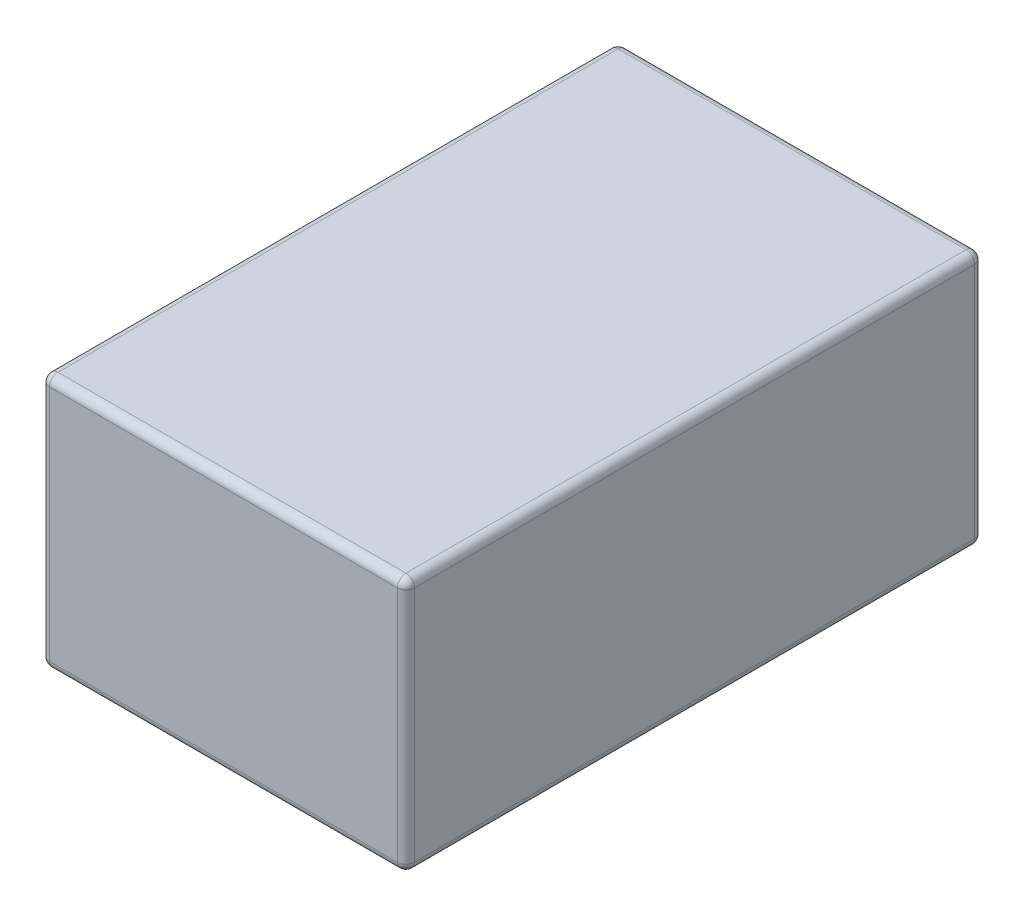
SolidWorks part; units mm, degrees
ref_plane "Front Plane" through (0, 0, 0) normal (0, 0, 1) x (1, 0, 0)
ref_plane "Top Plane" through (0, 0, 0) normal (0, 1, 0) x (1, 0, 0)
ref_plane "Right Plane" through (0, 0, 0) normal (1, 0, 0) x (0, 0, -1)
sketch "Sketch1" plane through (0, 0, 0) normal (0, 0, 1) x (1, 0, 0)
  line L1 (0, 0) -> (109.22, 0)
  line L2 (0, 0) -> (0, 76.2)
  line L3 (0, 76.2) -> (109.22, 76.2)
  line L4 (109.22, 0) -> (109.22, 76.2)
  dimension "D1" = 109.22
  dimension "D2" = 76.2
extrude "Boss-Extrude1" add sketch "Sketch1" along normal blind 172.72
fillet "Fillet1" radius 2.54 12 edges at (0, 38.1, 0) (109.22, 38.1, 0) (109.22, 38.1, 172.72) (0, 38.1, 172.72) (0, 0, 86.36) (54.61, 0, 172.72) (109.22, 0, 86.36) (54.61, 0, 0) (109.22, 76.2, 86.36) (54.61, 76.2, 172.72) (0, 76.2, 86.36) (54.61, 76.2, 0)
